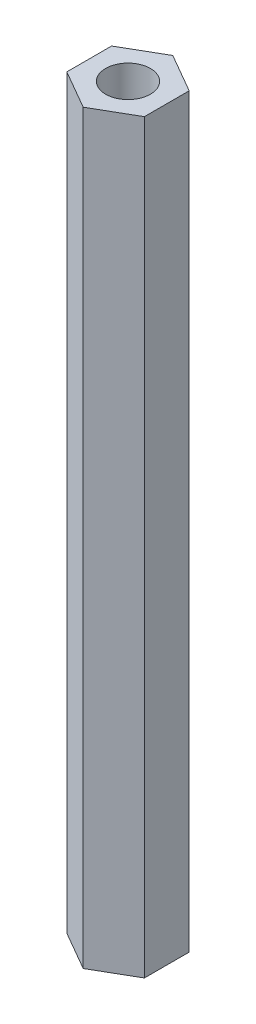
SolidWorks part; units mm, degrees
ref_plane "Front Plane" through (0, 0, 0) normal (0, 0, 1) x (1, 0, 0)
ref_plane "Top Plane" through (0, 0, 0) normal (0, 1, 0) x (1, 0, 0)
ref_plane "Right Plane" through (0, 0, 0) normal (1, 0, 0) x (0, 0, -1)
sketch "Sketch1" plane through (0, 0, 0) normal (0, 1, 0) x (1, 0, 0)
  line L0 (0, 0) -> (2.6, 0) construction
  line L1 (0, 3.0022) -> (-2.6, 1.5011)
  line L2 (-2.6, 1.5011) -> (-2.6, -1.5011)
  line L3 (-2.6, -1.5011) -> (0, -3.0022)
  line L4 (0, -3.0022) -> (2.6, -1.5011)
  line L5 (2.6, -1.5011) -> (2.6, 1.5011)
  line L6 (2.6, 1.5011) -> (0, 3.0022)
  circle A0 centre (0, 0) radius 1.5
  circle A1 centre (0, 0) radius 2.6 construction
  dimension "D1" = 3
  dimension "D2" = 2.6
extrude "Boss-Extrude2" add sketch "Sketch1" along normal blind 50
